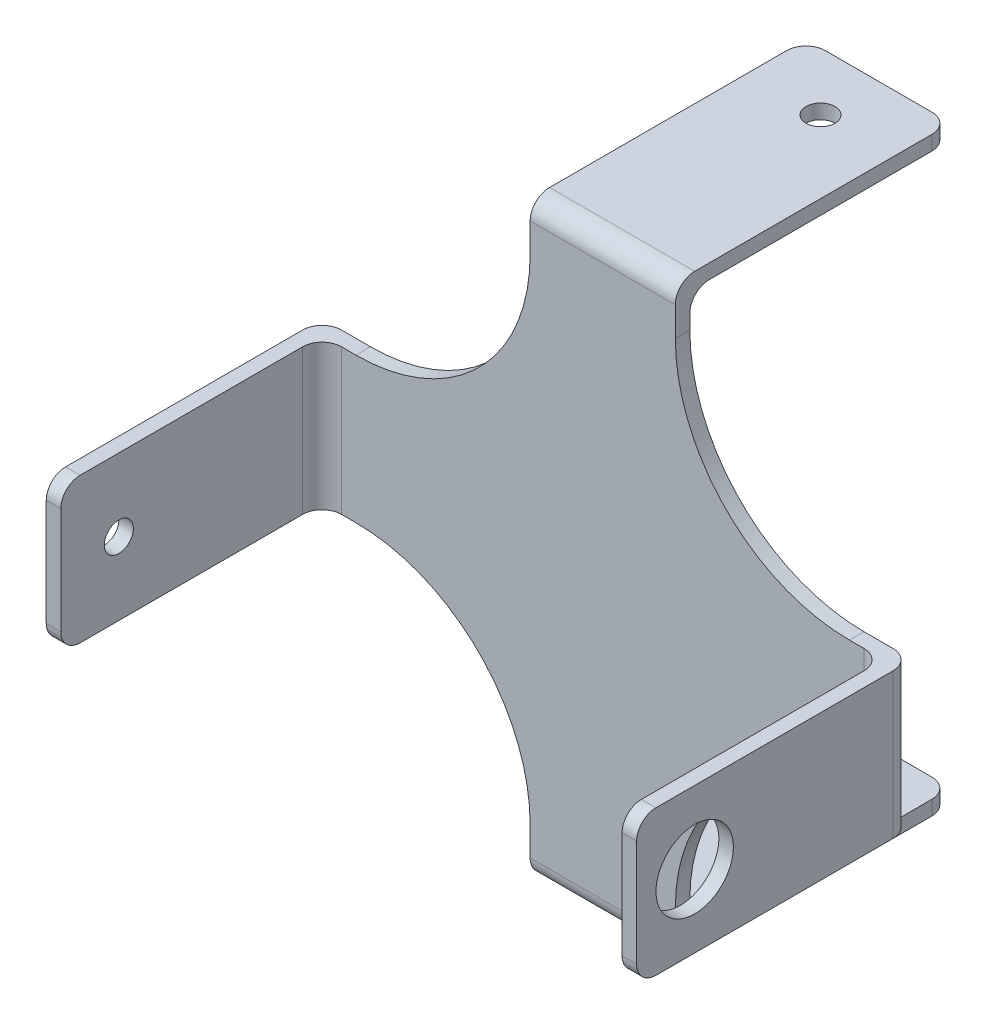
SolidWorks part; units mm, degrees
ref_plane "Front Plane" through (0, 0, 0) normal (0, 0, 1) x (1, 0, 0)
ref_plane "Top Plane" through (0, 0, 0) normal (0, 1, 0) x (1, 0, 0)
ref_plane "Right Plane" through (0, 0, 0) normal (1, 0, 0) x (0, 0, -1)
sketch "Sketch1" plane through (0, 0, 0) normal (0, 0, 1) x (1, 0, 0)
  line L1 (-29, -7.5) -> (29, -7.5)
  line L2 (-29, -7.5) -> (-29, 7.5)
  line L3 (-29, 7.5) -> (29, 7.5)
  line L4 (29, -7.5) -> (29, 7.5)
  line L5 (-29, -7.5) -> (29, 7.5) construction
  line L6 (-29, 7.5) -> (29, -7.5) construction
  line L9 (0, 7.5) -> (0, -7.5) construction
  line L10 (-29, 0) -> (29, 0) construction
  line L15 (-7.5, -29) -> (7.5, -29)
  line L16 (-7.5, -29) -> (-7.5, 29)
  line L17 (-7.5, 29) -> (7.5, 29)
  line L18 (7.5, -29) -> (7.5, 29)
  line L19 (-7.5, -29) -> (7.5, 29) construction
  line L20 (-7.5, 29) -> (7.5, -29) construction
  line L21 (-7.5, 29) -> (7.5, 29)
  point P0 (0, 0)
  point P18 (0, 0)
  dimension "D1" = 15
  dimension "D2" = 58
extrude "Boss-Extrude1" add sketch "Sketch1" along normal blind 1.5 contours L3 L18 L17 L16 | L1 L16 L3 L2 | L1 L18 L3 L16 | L18 L1 L4 L3 | L15 L18 L1 L16
sketch "Sketch2" plane through (0, 0, 1.5) normal (0, 0, 1) x (1, 0, 0)
  line L0 (0, 29) -> (0, -29) construction
  line L1 (-29, 7.5) -> (-30.5, 7.5)
  line L2 (-29, 7.5) -> (-29, -7.5)
  line L3 (-29, -7.5) -> (-30.5, -7.5)
  line L4 (-30.5, 7.5) -> (-30.5, -7.5)
  line L5 (30.5, 7.5) -> (30.5, -7.5)
  line L6 (29, -7.5) -> (30.5, -7.5)
  line L7 (29, 7.5) -> (29, -7.5)
  line L8 (29, 7.5) -> (30.5, 7.5)
  line L9 (-7.5, 29) -> (7.5, 29) construction
  line L10 (29, 0) -> (-29, 0) construction
  line L11 (29, -7.5) -> (29, 7.5) construction
  line L12 (-29, -7.5) -> (-7.5, -7.5) construction
  dimension "D1" = 1.5
extrude "Boss-Extrude2" add sketch "Sketch2" along normal blind 28.5 from offset 1.5 offset against normal yes
sketch "Sketch3" plane through (0, 0, 0) normal (0, 0, -1) x (-1, 0, 0)
  line L1 (7.5, 29) -> (-7.5, 29)
  line L2 (7.5, 29) -> (7.5, 30.5)
  line L3 (7.5, 30.5) -> (-7.5, 30.5)
  line L4 (-7.5, 29) -> (-7.5, 30.5)
  line L5 (7.5, -29) -> (-7.5, -29)
  line L6 (7.5, -29) -> (7.5, -30.5)
  line L7 (7.5, -30.5) -> (-7.5, -30.5)
  line L8 (-7.5, -29) -> (-7.5, -30.5)
  dimension "D1" = 1.5
  dimension "D2" = 1.5
extrude "Boss-Extrude3" add sketch "Sketch3" along normal blind 28.5 from offset 1.5 offset against normal yes
sketch "Sketch4" plane through (30.5, 0, 0) normal (1, 0, 0) x (0, 0, -1)
  line L0 (-28.5, -7.5) -> (-28.5, 7.5) construction
  circle A0 centre (-22.5, 0) radius 1.5
  dimension "D1" = 3
  dimension "D2" = 6
extrude "Cut-Extrude1" cut sketch "Sketch4" against normal through all
sketch "Sketch5" plane through (0, 30.5, 0) normal (0, 1, 0) x (1, 0, 0)
  line L0 (-7.5, 27) -> (7.5, 27) construction
  circle A0 centre (0, 21) radius 1.5
  dimension "D1" = 3
  dimension "D2" = 6
extrude "Cut-Extrude2" cut sketch "Sketch5" against normal through all
fillet "Fillet1" radius 2 8 edges at (-7.5, -29.75, -27) (7.5, -29.75, -27) (-7.5, 29.75, -27) (7.5, 29.75, -27) (-29.75, 7.5, 28.5) (-29.75, -7.5, 28.5) (29.75, -7.5, 28.5) (29.75, 7.5, 28.5)
fillet "Fillet2" radius 2 8 edges at (30.5, 0, 0) (-30.5, 0, 0) (0, -30.5, 1.5) (0, 30.5, 1.5)
fillet "Fillet3" radius 18 4 edges at (-7.5, 7.5, 0.75) (-7.5, -7.5, 0.75) (7.5, -7.5, 0.75) (7.5, 7.5, 0.75)
sketch "Sketch6" plane through (30.5, 0, 0) normal (1, 0, 0) x (0, 0, -1)
  circle A0 centre (-22.5, 0) radius 4
  dimension "D1" = 8
extrude "Cut-Extrude3" cut sketch "Sketch6" against normal up to next
sketch "Sketch7" plane through (0, -30.5, 0) normal (0, -1, 0) x (1, 0, 0)
  circle A0 centre (0, -21) radius 4
  dimension "D1" = 8
extrude "Cut-Extrude4" cut sketch "Sketch7" against normal up to next
